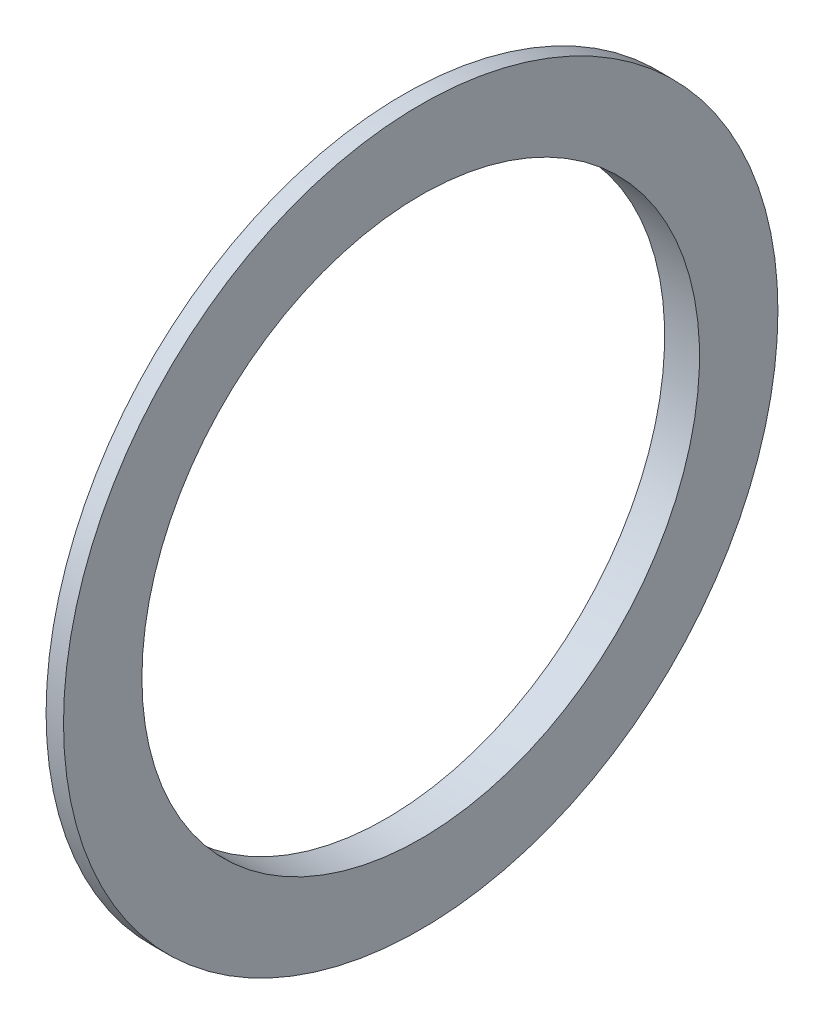
SolidWorks part; units mm, degrees
ref_plane "Płaszczyzna przednia" through (0, 0, 0) normal (0, 0, 1) x (1, 0, 0)
ref_plane "Płaszczyzna górna" through (0, 0, 0) normal (0, 1, 0) x (1, 0, 0)
ref_plane "Płaszczyzna prawa" through (0, 0, 0) normal (1, 0, 0) x (0, 0, -1)
sketch "Szkic1" plane through (0, 0, 0) normal (0, 0, 1) x (1, 0, 0)
  line L0 (153.3423, 16) -> (153.3423, 17.5)
  line L1 (153.3423, 17.5) -> (154.3423, 20.5)
  line L2 (154.3423, 20.5) -> (155.3423, 20.5)
  line L3 (155.3423, 20.5) -> (155.3423, 16)
  line L4 (213.7173, 16) -> (153.3423, 16) construction
  line L5 (155.3423, 16) -> (153.3423, 16)
  line L6 (0, 0) -> (168.3154, 0) construction
  dimension "D1" = 2
  dimension "D2" = 20.5
  dimension "D3" = 1
revolve "Obrót1" add sketch "Szkic1" angle 360 about L6
